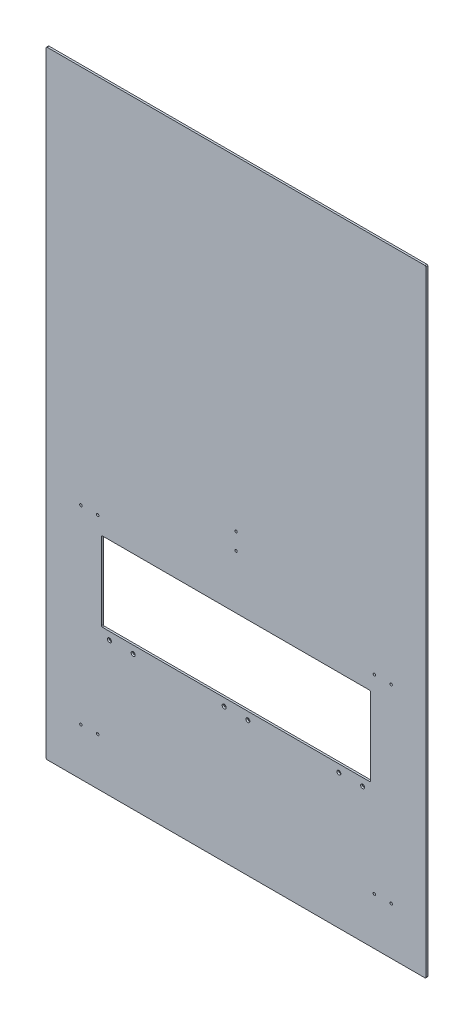
SolidWorks part; units mm, degrees
material "PC High Viscosity"
ref_plane "Front Plane" through (0, 0, 0) normal (0, 0, 1) x (1, 0, 0)
ref_plane "Top Plane" through (0, 0, 0) normal (0, 1, 0) x (1, 0, 0)
ref_plane "Right Plane" through (0, 0, 0) normal (1, 0, 0) x (0, 0, -1)
sketch "Sketch1" plane through (0, 0, 0) normal (0, 0, 1) x (1, 0, 0)
  line L1 (0, 0) -> (1219.2, 0)
  line L2 (0, 0) -> (0, 1981.2)
  line L3 (0, 1981.2) -> (1219.2, 1981.2)
  line L4 (1219.2, 0) -> (1219.2, 1981.2)
  line L5 (177.8, 457.2) -> (1041.4, 457.2)
  line L6 (177.8, 457.2) -> (177.8, 711.2)
  line L7 (177.8, 711.2) -> (1041.4, 711.2)
  line L8 (1041.4, 457.2) -> (1041.4, 711.2)
  point P9 (609.6, 0)
  point P10 (609.6, 457.2)
  dimension "D1" = 1219.2
  dimension "D2" = 1981.2
  dimension "D3" = 254
  dimension "D4" = 863.6
  dimension "D5" = 457.2
extrude "Boss-Extrude1" add sketch "Sketch1" along normal blind 6.35
hole_wizard "CSK for 1/4 Flat Head Machine Screw1" positions "Sketch2" profile "Sketch3" countersink size "1/4" standard "ANSI Inch" end condition through all
sketch "Sketch2" plane through (0, 0, 6.35) normal (0, 0, 1) x (1, 0, 0)
  ellipse E0 centre (571.5, 431.4641) end of major axis (569.2775, 431.4641) minor radius 0.9393 construction
  ellipse E1 centre (647.7, 431.4641) end of major axis (645.4775, 431.4641) minor radius 0.9393 construction
  point P355 (203.2, 432.3049)
  point P358 (279.4, 432.3049)
  point P361 (939.8, 432.5371)
  point P364 (1016, 432.5371)
  point P367 (571.5, 432.4033)
  point P375 (647.7, 432.4033)
sketch "Sketch3" plane through (203.2, 432.3049, 6.35) normal (1, 0, 0) x (0, -1, 0)
  line L0 (0, 0) -> (0, 6.35)
  line L1 (0, 6.35) -> (3.5712, 6.35)
  line L2 (3.5712, 6.35) -> (3.5712, 3.2989)
  line L3 (3.5712, 3.2989) -> (6.4389, 0)
  line L5 (6.4389, 0) -> (0, 0)
  line L6 (-3.5712, 3.2989) -> (-6.4389, 0) construction
  line L11 (0, -6.35) -> (0, 107.95) construction
  dimension "Thru Hole Dia." = 7.1425
  dimension "Thru Hole Depth" = 6.35
  dimension "Near C'Sink Dia." = 12.8778
  dimension "Near C'Sink Angle" = 82
fillet "Fillet1" radius 3.175 8 edges at (1219.2, 1981.2, 3.175) (0, 1981.2, 3.175) (0, 0, 3.175) (1219.2, 0, 3.175) (1041.4, 457.2, 3.175) (1041.4, 711.2, 3.175) (177.8, 457.2, 3.175) (177.8, 711.2, 3.175)
hole_wizard "5/16 (0.3125) Diameter Hole2" positions "Sketch5" profile "Sketch6" hole size "5/16" standard "ANSI Inch" end condition through all
sketch "Sketch5" plane through (0, 0, 6.35) normal (0, 0, 1) x (1, 0, 0)
  line L0 (609.6, 0) -> (609.6, 1981.2) construction
  line L1 (3.175, 0) -> (1216.025, 0) construction
  line L2 (1216.025, 1981.2) -> (3.175, 1981.2) construction
  line L3 (1219.2, 44.45) -> (0, 44.45) construction
  line L4 (1219.2, 3.175) -> (1219.2, 1978.025) construction
  line L5 (0, 1978.025) -> (0, 3.175) construction
  line L8 (0, 933.45) -> (1219.2, 933.45) construction
  line L9 (0, 933.45) -> (0, 889) construction
  line L10 (0, 889) -> (1219.2, 889) construction
  line L11 (1219.2, 933.45) -> (1219.2, 889) construction
  line L13 (117.475, 889) -> (159.639, 889) construction
  line L14 (117.475, 889) -> (117.475, 44.45) construction
  line L15 (117.475, 44.45) -> (159.639, 44.45) construction
  line L16 (159.639, 889) -> (159.639, 44.45) construction
  line L17 (1101.725, 44.45) -> (1059.561, 44.45) construction
  line L19 (1101.725, 889) -> (1059.561, 889) construction
  line L21 (138.557, 44.45) -> (138.557, 889) construction
  line L22 (1219.2, 911.225) -> (0, 911.225) construction
  point P167 (609.6, 44.45)
  point P181 (111.5695, 762)
  point P183 (111.5695, 152.4)
  point P188 (165.5445, 152.4)
  point P189 (165.5445, 762)
  point P192 (1053.6555, 152.4)
  point P193 (1107.6305, 152.4)
  point P194 (1107.6305, 762)
  point P195 (1053.6555, 762)
  point P197 (609.6, 884.2375)
  point P199 (609.6, 938.2125)
  point P205 (0, 0)
  dimension "D1" = 44.45
  dimension "D2" = 44.45
  dimension "D3" = 42.164
  dimension "D4" = 117.475
  dimension "D5" = 933.45
  dimension "D6" = 53.975
  dimension "D7" = 762
  dimension "D8" = 152.4
  dimension "D9" = 53.975
sketch "Sketch6" plane through (609.6, 938.2125, 6.35) normal (1, 0, 0) x (0, -1, 0)
  line L0 (0, 0) -> (0, 6.35)
  line L1 (0, 6.35) -> (3.9687, 6.35)
  line L2 (3.9687, 6.35) -> (3.9687, 0)
  line L5 (3.9687, 0) -> (0, 0)
  line L11 (0, -6.35) -> (0, 107.95) construction
  dimension "Thru Hole Dia." = 7.9375
  dimension "Thru Hole Depth" = 6.35
